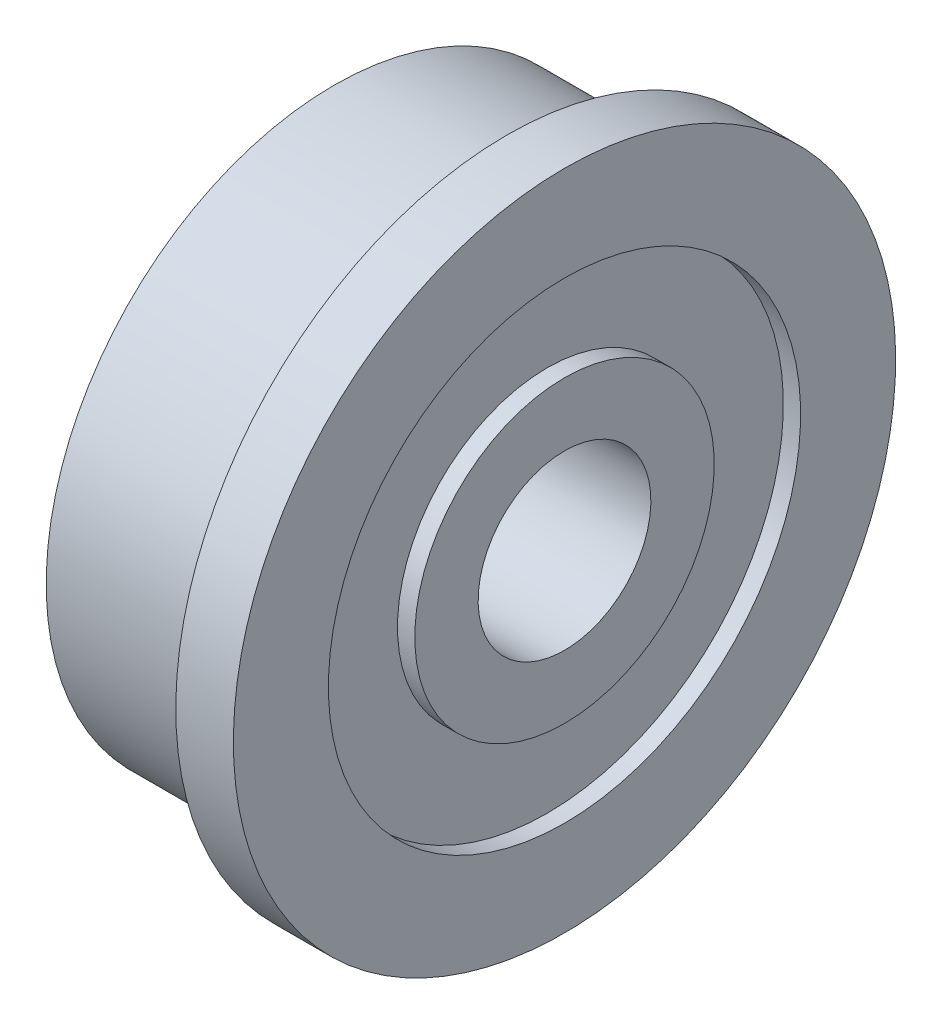
SolidWorks part; units mm, degrees
material "Plain Carbon Steel"
ref_plane "Front Plane" through (0, 0, 0) normal (0, 0, 1) x (1, 0, 0)
ref_plane "Top Plane" through (0, 0, 0) normal (0, 1, 0) x (1, 0, 0)
ref_plane "Right Plane" through (0, 0, 0) normal (1, 0, 0) x (0, 0, -1)
sketch "Sketch1" plane through (0, 0, 0) normal (0, 0, 1) x (1, 0, 0)
  line L0 (2, 1.5) -> (-2, 1.5)
  line L1 (-2, 1.5) -> (-2, 2.6)
  line L2 (-2, 2.6) -> (-1.7, 2.6)
  line L3 (-1.7, 2.6) -> (-1.7, 4.1)
  line L4 (-1.7, 4.1) -> (-2, 4.1)
  line L5 (-2, 4.1) -> (-2, 5)
  line L6 (1, 5) -> (-2, 5)
  line L7 (0, 5) -> (0, 1.5) construction
  line L8 (2, 4.1) -> (2, 5.75)
  line L9 (1.7, 4.1) -> (2, 4.1)
  line L10 (1.7, 2.6) -> (1.7, 4.1)
  line L11 (2, 2.6) -> (1.7, 2.6)
  line L12 (2, 1.5) -> (2, 2.6)
  line L13 (0, 0) -> (-5.75, 0) construction
  line L15 (2, 5.75) -> (1, 5.75)
  line L16 (1, 5.75) -> (1, 5)
  dimension "D1" = 3
  dimension "D2" = 1
  dimension "D3" = 4
  dimension "D4" = 5.2
  dimension "D5" = 1.5
  dimension "D6" = 0.3
  dimension "D7" = 5.75
  dimension "D8" = 5
revolve "Revolve1" add sketch "Sketch1" angle 360 about L13
